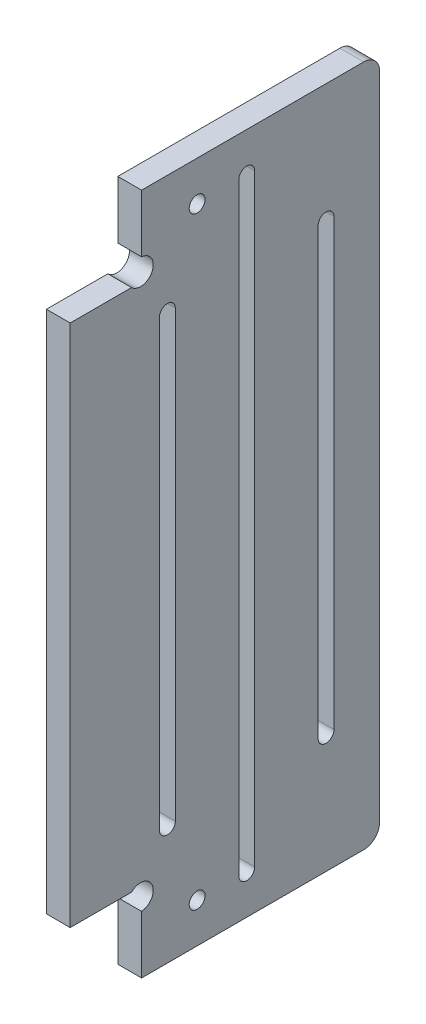
SolidWorks part; units mm, degrees
ref_plane "Plan de face" through (0, 0, 0) normal (0, 0, 1) x (1, 0, 0)
ref_plane "Plan de dessus" through (0, 0, 0) normal (0, 1, 0) x (1, 0, 0)
ref_plane "Plan de droite" through (0, 0, 0) normal (1, 0, 0) x (0, 0, -1)
sketch "Esquisse1" plane through (0, 0, 0) normal (1, 0, 0) x (0, 0, -1)
  line L4 (109, 226.8628) -> (79, 226.8628)
  line L6 (77.7373, 150.8628) -> (70, 150.8628)
  line L8 (77.7373, 216.8628) -> (70, 216.8628)
  line L9 (79, 140.8628) -> (79, 148.1369)
  line L12 (70, 150.8628) -> (70, 216.8628)
  line L13 (79, 219.5888) -> (79, 226.8628)
  line L46 (79, 140.8628) -> (109, 140.8628)
  line L49 (109, 140.8628) -> (109, 226.8628)
  arc A0 (79, 148.1369) -> (77.7373, 150.8628) centre (78.8686, 149.7315) ccw
  arc A1 (79, 219.5888) -> (77.7373, 216.8628) centre (78.8686, 217.9942) cw
  dimension "D4" = 10
  dimension "D12" = 30
  dimension "D7" = 8.8686
  dimension "D9" = 86
  dimension "D11" = 1.6
  dimension "D2" = 1.6
  dimension "D3" = 9
  dimension "D5" = 9
  dimension "D6" = 8.8686
  dimension "D8" = 8.8686
  dimension "D10" = 10
extrude "Extrusion1" add sketch "Esquisse1" along normal blind 3
sketch "Esquisse3" plane through (0, 0, 0) normal (-1, 0, 0) x (0, 0, 1)
  line L0 (-82.25, 155.8628) -> (-82.25, 211.8628) construction
  line L1 (-83.25, 155.8628) -> (-83.25, 211.8628)
  line L2 (-81.25, 155.8628) -> (-81.25, 211.8628)
  line L3 (-92.25, 145.8628) -> (-92.25, 221.8628) construction
  line L4 (-93.25, 145.8628) -> (-93.25, 221.8628)
  line L5 (-91.25, 145.8628) -> (-91.25, 221.8628)
  line L6 (-102.25, 155.8628) -> (-102.25, 211.8628) construction
  line L7 (-103.25, 155.8628) -> (-103.25, 211.8628)
  line L8 (-101.25, 155.8628) -> (-101.25, 211.8628)
  line L9 (-79, 140.8628) -> (-109, 140.8628) construction
  line L10 (-109, 226.8628) -> (-79, 226.8628) construction
  line L11 (-79, 148.1369) -> (-79, 140.8628) construction
  arc A0 (-83.25, 155.8628) -> (-81.25, 155.8628) centre (-82.25, 155.8628) ccw
  arc A1 (-81.25, 211.8628) -> (-83.25, 211.8628) centre (-82.25, 211.8628) ccw
  arc A2 (-93.25, 145.8628) -> (-91.25, 145.8628) centre (-92.25, 145.8628) ccw
  arc A3 (-91.25, 221.8628) -> (-93.25, 221.8628) centre (-92.25, 221.8628) ccw
  arc A4 (-103.25, 155.8628) -> (-101.25, 155.8628) centre (-102.25, 155.8628) ccw
  arc A5 (-101.25, 211.8628) -> (-103.25, 211.8628) centre (-102.25, 211.8628) ccw
  point P2 (-82.25, 183.8628)
  point P7 (-92.25, 183.8628)
  point P14 (-102.25, 183.8628)
  dimension "D1" = 1
  dimension "D2" = 1
  dimension "D3" = 1
  dimension "D4" = 15
  dimension "D5" = 15
  dimension "D6" = 3.25
  dimension "D7" = 10
  dimension "D8" = 10
  dimension "D9" = 5
  dimension "D10" = 5
extrude "Enlèv. mat.-Extru.2" cut sketch "Esquisse3" against normal through all
sketch "Esquisse4" plane through (0, 0, 0) normal (-1, 0, 0) x (0, 0, 1)
  line L0 (-79, 140.8628) -> (-109, 140.8628) construction
  line L1 (-79, 148.1369) -> (-79, 140.8628) construction
  line L4 (-109, 226.8628) -> (-79, 226.8628) construction
  circle A2 centre (-86, 221.8628) radius 1
  circle A3 centre (-86, 145.8628) radius 1
  dimension "D1" = 2
  dimension "D2" = 5
  dimension "D3" = 7
  dimension "D4" = 5
extrude "Enlèv. mat.-Extru.3" cut sketch "Esquisse4" against normal through all
fillet "Congé1" radius 2 2 edges at (1.5, 226.8628, -109) (1.5, 140.8628, -109)
